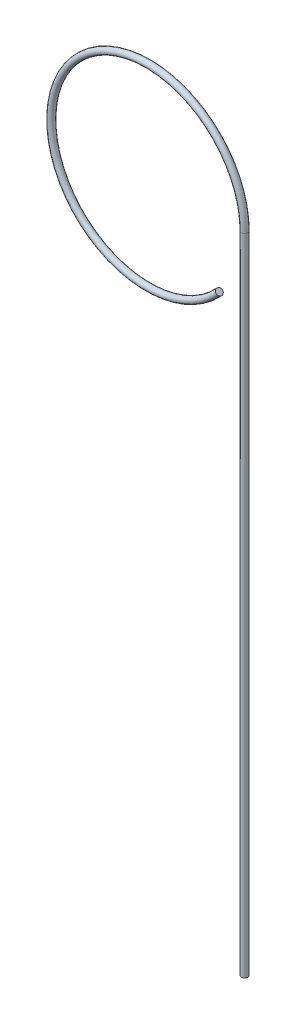
SolidWorks part; units mm, degrees
ref_plane "Front Plane" through (0, 0, 0) normal (0, 0, 1) x (1, 0, 0)
ref_plane "Top Plane" through (0, 0, 0) normal (0, 1, 0) x (1, 0, 0)
ref_plane "Right Plane" through (0, 0, 0) normal (1, 0, 0) x (0, 0, -1)
sketch "Sketch1" plane through (0, 0, 0) normal (0, 0, 1) x (1, 0, 0)
  line L0 (30, 0) -> (30, -100)
  arc A1 (22.1333, -20.2513) -> (30, 0) centre (0, 0) cw
  dimension "D1" = 100
ref_plane "Plane1" through (0, -100, 0) normal (0, 1, 0) x (1, 0, 0)
sketch "Sketch3" plane through (0, -100, 0) normal (0, 1, 0) x (1, 0, 0)
  circle A0 centre (30, 0) radius 1
  dimension "D1" = 2
sweep "Sweep2" add profiles "Sketch3" path "Sketch1"
sketch "Sketch4" plane through (0, -100, 0) normal (0, -1, 0) x (1, 0, 0)
  circle A0 centre (30, 0) radius 1
extrude "Boss-Extrude1" add sketch "Sketch4" along normal blind 100
